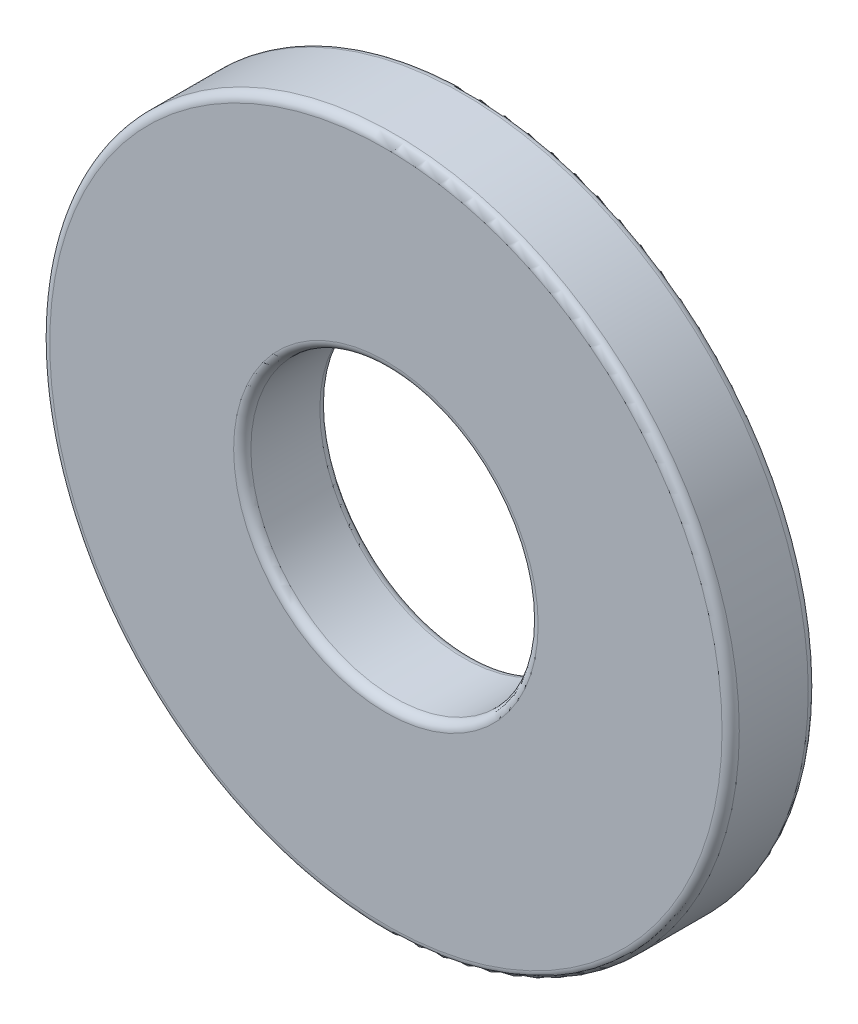
SolidWorks part; units mm, degrees
ref_plane "Front Plane" through (0, 0, 0) normal (0, 0, 1) x (1, 0, 0)
ref_plane "Top Plane" through (0, 0, 0) normal (0, 1, 0) x (1, 0, 0)
ref_plane "Right Plane" through (0, 0, 0) normal (1, 0, 0) x (0, 0, -1)
sketch "Sketch1" plane through (0, 0, 0) normal (0, 0, 1) x (1, 0, 0)
  circle A0 centre (0, 0) radius 2.5
  circle A1 centre (0, 0) radius 6
  dimension "D1" = 5
  dimension "D2" = 12
extrude "Boss-Extrude1" add sketch "Sketch1" along normal blind 1.5
fillet "Fillet1" radius 0.15 4 edges at (2.5, 0, 0) (6, 0, 0) (2.5, 0, 1.5) (6, 0, 1.5)
